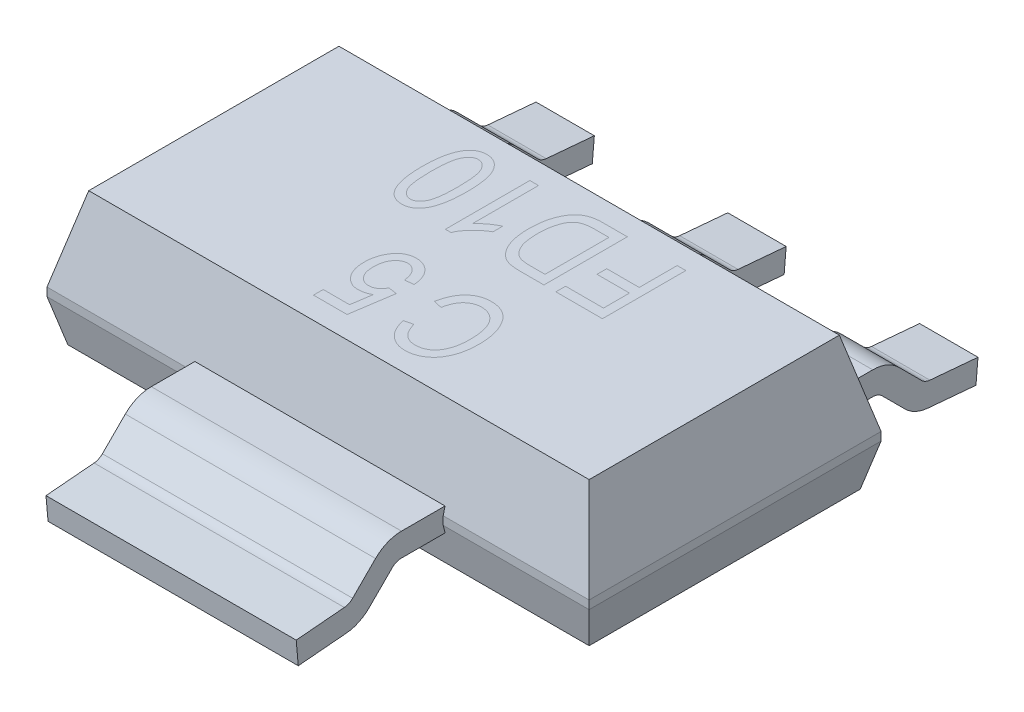
SolidWorks part; units mm, degrees
material "Pure Silver"
ref_plane "Front Plane" through (0, 0, 0) normal (0, 0, 1) x (1, 0, 0)
ref_plane "Top Plane" through (0, 0, 0) normal (0, 1, 0) x (1, 0, 0)
ref_plane "Right Plane" through (0, 0, 0) normal (1, 0, 0) x (0, 0, -1)
sketch "Sketch1" plane through (0, 0, 0) normal (0, 1, 0) x (1, 0, 0)
  line L0 (0, -55) -> (0, 55) construction
  line L1 (-3.25, 1.75) -> (3.25, 1.75)
  line L2 (-3.25, 1.75) -> (-3.25, -1.75)
  line L3 (-3.25, -1.75) -> (3.25, -1.75)
  line L4 (3.25, 1.75) -> (3.25, -1.75)
  line L5 (-55, 0) -> (55, 0) construction
  dimension "D1" = 6.5
  dimension "D2" = 3.25
  dimension "D3" = 3.5
  dimension "D4" = 1.75
extrude "Boss-Extrude1" add sketch "Sketch1" along normal blind 1.6
chamfer "Chamfer1" distance 1 distance2 0.25 4 edges at (-3.25, 1.6, 0) (0, 1.6, -1.75) (3.25, 1.6, 0) (0, 1.6, 1.75)
chamfer "Chamfer2" distance 0.125 distance2 0.5 4 edges at (0, 0, 1.75) (-3.25, 0, 0) (0, 0, -1.75) (3.25, 0, 0)
sketch "Sketch2" plane through (0, 0, 0) normal (1, 0, 0) x (0, 0, -1)
  line L0 (0, 0.55) -> (-2.25, 0.55)
  line L1 (0, 0.88) -> (0, -0.88) construction
  line L2 (-2.4621, 0.4621) -> (-2.7371, 0.1872)
  line L3 (-2.923, 0.1005) -> (-3.5, 0.05)
  line L4 (1.925, 0) -> (-1.925, 0) construction
  arc A0 (-2.25, 0.55) -> (-2.4621, 0.4621) centre (-2.25, 0.25) ccw
  arc A1 (-2.7371, 0.1872) -> (-2.923, 0.1005) centre (-2.9492, 0.3993) cw
  dimension "D4" = 0.3
  dimension "D1" = 0.55
  dimension "D2" = 3.5
  dimension "D3" = 0.05
  dimension "D5" = 45
  dimension "D6" = 5
  dimension "D7" = 2.25
extrude "Extrude-Thin1" add sketch "Sketch2" along normal mid plane 3 thin thin type mid plane wall 0.28
ref_plane "Plane1" through (2.3, 0, 0) normal (1, 0, 0) x (0, 0, -1)
sketch "Sketch3" plane through (2.3, 0, 0) normal (1, 0, 0) x (0, 0, -1)
  line L0 (0, 0.55) -> (2.25, 0.55)
  line L1 (0, 0.88) -> (0, -0.88) construction
  line L2 (2.4621, 0.4621) -> (2.7371, 0.1872)
  line L3 (2.923, 0.1005) -> (3.5, 0.05)
  line L4 (0, 0.55) -> (-2.25, 0.55) construction
  arc A0 (2.7371, 0.1872) -> (2.923, 0.1005) centre (2.9492, 0.3993) ccw
  arc A1 (2.25, 0.55) -> (2.4621, 0.4621) centre (2.25, 0.25) cw
  dimension "D2" = 0.3
  dimension "D1" = 3.5
  dimension "D3" = 2.25
  dimension "D4" = 45
extrude "Extrude-Thin2" add sketch "Sketch3" along normal mid plane 0.7 thin thin type mid plane wall 0.28
pattern_linear "LPattern1" count 3 spacing 2.3 along (-1, 0, 0) of "Extrude-Thin2"
sketch "Sketch5" plane through (0, 1.6, 0) normal (0, 1, 0) x (1, 0, 0)
  line L0 (1, -0.25) -> (-2.199, -0.25) construction
  line L1 (0, -0.9292) -> (0, 0.9292) construction
  line L2 (-0.88, 0) -> (0.88, 0) construction
  text T0 "C5" font "Arial Narrow" height 1
  dimension "D1" = 1
  dimension "D2" = 0.25
sketch "Sketch6" plane through (0, 1.6, 0) normal (0, 1, 0) x (1, 0, 0)
  line L0 (1.5, 1.25) -> (-2.6137, 1.25) construction
  line L1 (-0.88, 0) -> (0.88, 0) construction
  line L2 (0, -0.9292) -> (0, 0.9292) construction
  text T0 "FD10" font "Arial Narrow" height 1
  dimension "D1" = 1.25
  dimension "D2" = 1.5
split line "Split Line1"
split line "Split Line2"
